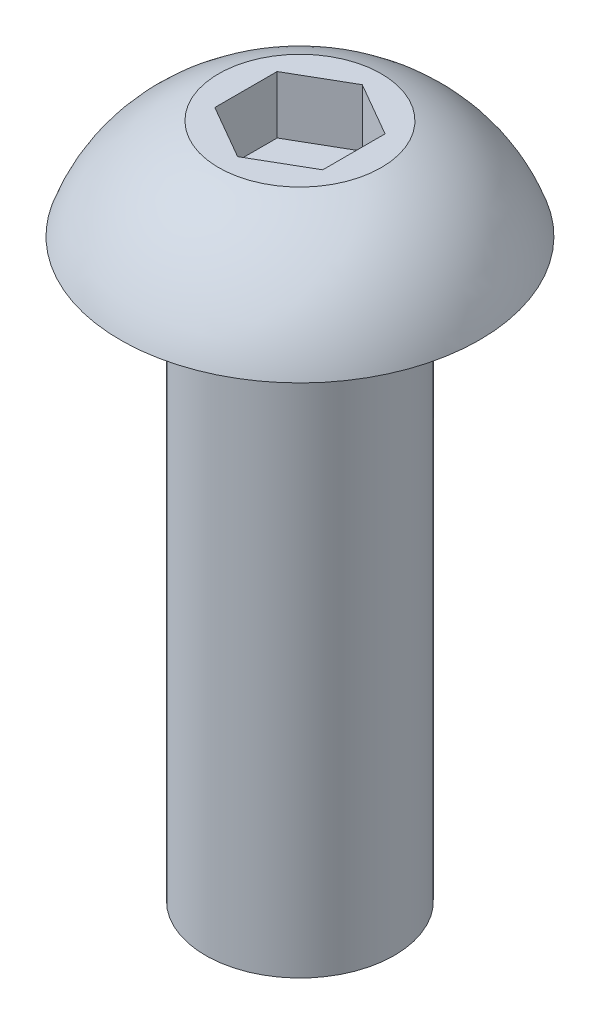
SolidWorks part; units mm, degrees
material "AISI Type 316L stainless steel"
ref_plane "Front Plane" through (0, 0, 0) normal (0, 0, 1) x (1, 0, 0)
ref_plane "Top Plane" through (0, 0, 0) normal (0, 1, 0) x (1, 0, 0)
ref_plane "Right Plane" through (0, 0, 0) normal (1, 0, 0) x (0, 0, -1)
sketch "Sketch1" plane through (0, 0, 0) normal (0, 0, 1) x (1, 0, 0)
  line L0 (-2.0828, 0) -> (-3.9624, 0)
  line L1 (-2.0828, 0) -> (-2.0828, -12.7)
  line L2 (0, -12.7) -> (0, 2.2098)
  line L3 (0, 2.2098) -> (-1.7948, 2.2098)
  line L4 (-2.0828, -12.7) -> (0, -12.7)
  arc A0 (-3.9624, 0) -> (-1.7948, 2.2098) centre (-0.5889, -1.1411) cw
  dimension "D1" = 12.7
  dimension "D2" = 2.2098
  dimension "D3" = 3.9624
  dimension "D4" = 2.0828
  dimension "D5" = 1.7948
revolve "Revolve1" add sketch "Sketch1" angle 360 about L2
sketch "Sketch2" plane through (0, 2.2098, 0) normal (0, 1, 0) x (1, 0, 0)
  line L0 (0, 0) -> (0, 1.3748) construction
  line L1 (-1.1906, 0.6874) -> (-1.1906, -0.6874)
  line L2 (-1.1906, -0.6874) -> (0, -1.3748)
  line L3 (0, -1.3748) -> (1.1906, -0.6874)
  line L4 (1.1906, -0.6874) -> (1.1906, 0.6874)
  line L5 (1.1906, 0.6874) -> (0, 1.3748)
  line L6 (0, 1.3748) -> (-1.1906, 0.6874)
  circle A0 centre (0, 0) radius 1.1906 construction
  dimension "D1" = 2.3813
extrude "Cut-Extrude1" cut sketch "Sketch2" against normal blind 1.27
